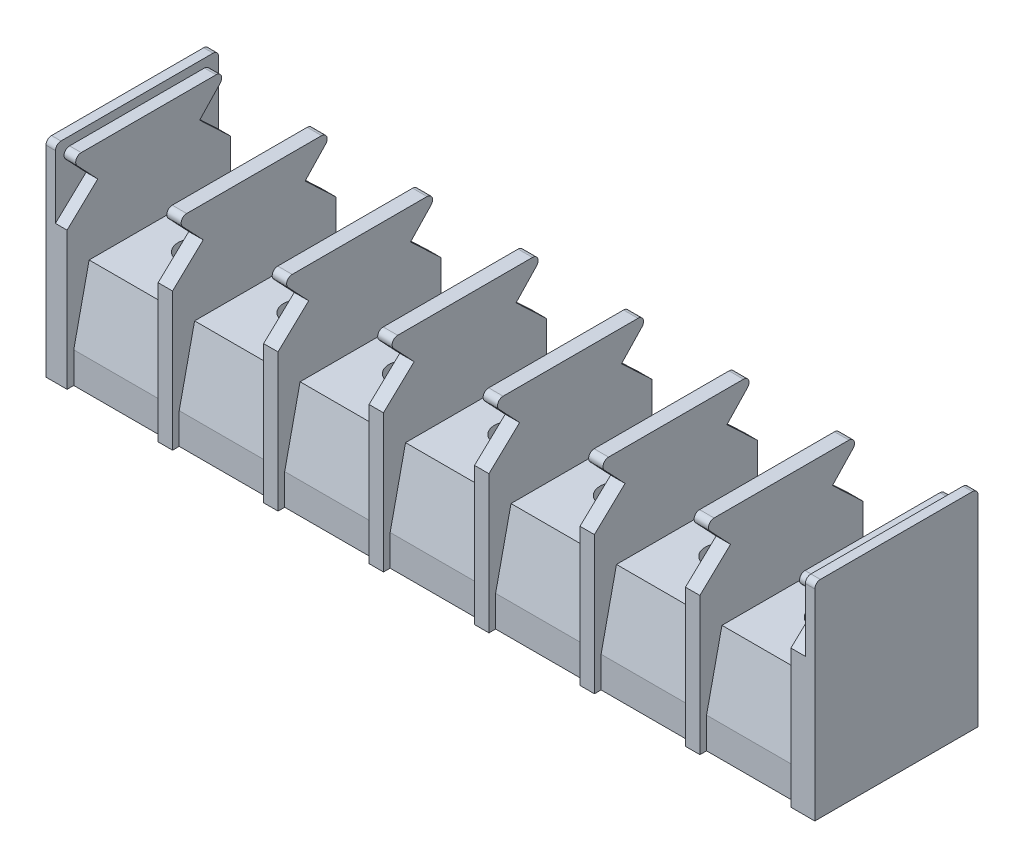
SolidWorks part; units mm, degrees
material "6061 Alloy"
ref_plane "Front Plane" through (0, 0, 0) normal (0, 0, 1) x (1, 0, 0)
ref_plane "Top Plane" through (0, 0, 0) normal (0, 1, 0) x (1, 0, 0)
ref_plane "Right Plane" through (0, 0, 0) normal (1, 0, 0) x (0, 0, -1)
sketch "Sketch1" plane through (0, 0, 0) normal (1, 0, 0) x (0, 0, -1)
  line L0 (6.75, 0) -> (7.35, 0) construction
  line L1 (-7.35, 0) -> (-6.75, 0) construction
  line L2 (-7.35, 0) -> (-7.35, 18.6) construction
  line L3 (-7.35, 18.6) -> (7.35, 18.6) construction
  line L4 (7.35, 0) -> (7.35, 18.6) construction
  line L5 (6.75, 0) -> (6.75, 2.79)
  line L6 (-6.75, 0) -> (-6.75, 2.79)
  line L7 (-6.75, 2.79) -> (-5.365, 9.1)
  line L8 (-5.365, 9.1) -> (5.365, 9.1)
  line L9 (5.365, 9.1) -> (6.75, 2.79)
  line L10 (-6.75, 0) -> (6.75, 0)
  line L11 (-6.75, 2.79) -> (6.75, 2.79) construction
  dimension "D1" = 18.6
  dimension "D2" = 14.7
  dimension "D3" = 1.2
  dimension "D4" = 10.73
  dimension "D5" = 9.1
  dimension "D6" = 2.79
extrude "Boss-Extrude1" add sketch "Sketch1" along normal mid plane 69.25
sketch "Sketch3" plane through (34.625, 0, 0) normal (1, 0, 0) x (0, 0, -1)
  line L0 (-6.75, 0) -> (-7.35, 0)
  line L1 (6.75, 0) -> (7.35, 0)
  line L2 (7.35, 0) -> (7.35, 18.1)
  line L3 (6.85, 18.6) -> (-6.85, 18.6)
  line L4 (-7.35, 18.1) -> (-7.35, 0)
  line L6 (-6.75, 0) -> (6.75, 0)
  line L7 (6.75, 0) -> (6.75, 2.79)
  line L8 (6.75, 2.79) -> (5.365, 9.1)
  line L9 (5.365, 9.1) -> (-5.365, 9.1)
  line L10 (-5.365, 9.1) -> (-6.75, 2.79)
  line L11 (-6.75, 2.79) -> (-6.75, 0)
  line L13 (6.75, 0) -> (6.75, 2.79)
  line L14 (6.75, 2.79) -> (5.365, 9.1)
  line L15 (5.365, 9.1) -> (-5.365, 9.1)
  line L16 (-5.365, 9.1) -> (-6.75, 2.79)
  line L17 (-6.75, 2.79) -> (-6.75, 0)
  arc A0 (6.85, 18.6) -> (7.35, 18.1) centre (6.85, 18.1) cw
  arc A1 (-6.85, 18.6) -> (-7.35, 18.1) centre (-6.85, 18.1) ccw
  point P13 (7.35, 18.6)
  point P16 (-7.35, 18.6)
  dimension "D4" = 0.5
  dimension "D2" = 18.6
  dimension "D3" = 14.7
  dimension "D1" = 0
extrude "Boss-Extrude2" add sketch "Sketch3" against normal blind 0.85
mirror "Mirror1" about plane through (0, 0, 0) normal (1, 0, 0) of "Boss-Extrude2"
sketch "Sketch4" plane through (33.775, 0, 0) normal (-1, 0, 0) x (0, 0, 1)
  line L0 (-7.35, 0) -> (-7.35, 18.1) construction
  line L1 (7.35, 18.1) -> (7.35, 0) construction
  line L2 (-6.75, 2.79) -> (-6.75, 0) construction
  line L3 (7.35, 12.42) -> (7.35, 0)
  line L4 (7.35, 0) -> (6.75, 0) construction
  line L5 (-5.365, 9.1) -> (-6.75, 2.79) construction
  line L6 (-7.35, 12.42) -> (-4.5889, 15.03)
  line L7 (7.35, 12.42) -> (4.5889, 15.03)
  line L8 (4.5889, 15.03) -> (6.4384, 16.9865)
  line L9 (-4.5889, 15.03) -> (-6.4384, 16.9865)
  line L10 (-6.75, 0) -> (-7.35, 0) construction
  line L11 (-7.35, 12.42) -> (7.35, 12.42) construction
  line L12 (-6.075, 17.83) -> (6.075, 17.83)
  line L13 (-7.35, 0) -> (-7.35, 12.42)
  line L14 (-6.75, 0) -> (-7.35, 0)
  line L15 (7.35, 0) -> (6.75, 0)
  line L16 (5.365, 9.1) -> (-5.365, 9.1) construction
  line L17 (-6.85, 18.6) -> (6.85, 18.6) construction
  line L18 (-6.75, 2.79) -> (-6.75, 0)
  line L19 (-5.365, 9.1) -> (-6.75, 2.79)
  line L20 (5.365, 9.1) -> (-5.365, 9.1)
  line L21 (6.75, 0) -> (6.75, 2.79) construction
  line L22 (6.75, 2.79) -> (5.365, 9.1) construction
  line L23 (6.75, 0) -> (6.75, 2.79)
  line L24 (6.75, 2.79) -> (5.365, 9.1)
  line L25 (-6.575, 12.42) -> (-6.575, 18.6) construction
  line L26 (-6.85, 18.6) -> (6.85, 18.6) construction
  line L27 (6.575, 12.42) -> (6.575, 18.6) construction
  arc A3 (6.075, 17.83) -> (6.4384, 16.9865) centre (6.075, 17.33) cw
  arc A4 (-6.075, 17.83) -> (-6.4384, 16.9865) centre (-6.075, 17.33) ccw
  arc A5 (-6.075, 17.83) -> (-6.4384, 16.9865) centre (-6.075, 17.33) ccw
  line M1 (6.75, 2.79) -> (6.75, 0)
  line M2 (6.75, 0) -> (7.35, 0)
  line M3 (7.35, 0) -> (7.35, 18.1)
  line M7 (-7.35, 18.1) -> (-7.35, 0)
  line M8 (-7.35, 0) -> (-6.75, 0)
  line M9 (-6.75, 0) -> (-6.75, 2.79)
  line M10 (-6.75, 2.79) -> (-5.365, 9.1)
  line M11 (-5.365, 9.1) -> (5.365, 9.1)
  line M12 (5.365, 9.1) -> (6.75, 2.79)
  dimension "D3" = 0.5
  dimension "D1" = 12.42
  dimension "D2" = 0.77
  dimension "D4" = 2.8
  dimension "D5" = 13.15
extrude "Boss-Extrude3" add sketch "Sketch4" along normal blind 1.3 contours L12 A4 L9 L6 L7 L8 A3 M7 M8 M9 M10 M11 M12 M1 M2 M3
pattern_linear "LPattern1" count 8 spacing 9.5 along (-1, 0, 0) of "Boss-Extrude3"
hole_wizard "M3.5x0.6 Tapped Hole1" positions "Sketch6" profile "Sketch5" tap size "M3.5x0.6" standard "ANSI Metric"
sketch "Sketch6" plane through (0, 9.1, 0) normal (0, 1, 0) x (1, 0, 0)
  line L12 (-32.725, 0) -> (-24.525, 0) construction
  line L14 (-24.525, 5.365) -> (-24.525, -5.365) construction
  line L15 (-23.225, 0) -> (-15.025, 0) construction
  line L17 (-15.025, 5.365) -> (-15.025, -5.365) construction
  line L21 (-4.225, 0) -> (3.975, 0) construction
  line L22 (-4.225, 5.365) -> (-4.225, -5.365) construction
  line L24 (5.275, 0) -> (13.475, 0) construction
  line L26 (13.475, 5.365) -> (13.475, -5.365) construction
  line L27 (14.775, 0) -> (22.975, 0) construction
  line L28 (14.775, 5.365) -> (14.775, -5.365) construction
  line L30 (24.275, 0) -> (32.475, 0) construction
  line L32 (32.475, 5.365) -> (32.475, -5.365) construction
  line L35 (-32.725, 5.365) -> (-32.725, -5.365) construction
  line L36 (-23.225, 5.365) -> (-23.225, -5.365) construction
  line L37 (3.975, 5.365) -> (3.975, -5.365) construction
  line L38 (5.275, 5.365) -> (5.275, -5.365) construction
  line L39 (22.975, 5.365) -> (22.975, -5.365) construction
  line L40 (24.275, 5.365) -> (24.275, -5.365) construction
  line L41 (-13.725, 0) -> (-5.525, 0) construction
  line L42 (-5.525, 5.365) -> (-5.525, -5.365) construction
  line L43 (-13.725, 5.365) -> (-13.725, -5.365) construction
  point P4 (-28.625, 0)
  point P6 (-19.125, 0)
  point P8 (0, 0)
  point P11 (-0.125, 0)
  point P13 (9.375, 0)
  point P15 (18.875, 0)
  point P17 (28.375, 0)
  point P134 (-9.625, 0)
sketch "Sketch5" plane through (-28.625, 9.1, 0) normal (1, 0, 0) x (0, 0, 1)
  line L0 (0, 0) -> (0, 8.8712)
  line L1 (0, 8.8712) -> (1.45, 8)
  line L2 (1.45, 8) -> (1.45, 0)
  line L5 (1.45, 0) -> (0, 0)
  line L10 (0, 8.8712) -> (-1.45, 8) construction
  line L11 (0, -6.35) -> (0, 107.95) construction
  dimension "Tap Drill Dia." = 2.9
  dimension "Tap Drill Depth" = 8
  dimension "Drill Angle" = 118
cosmetic thread "Hole Thread1" parameters "D1"=6, "D2"=3.5
cosmetic thread "Hole Thread2" parameters "D1"=6, "D2"=3.5
cosmetic thread "Hole Thread3" parameters "D1"=6, "D2"=3.5
cosmetic thread "Hole Thread4" parameters "D1"=6, "D2"=3.5
cosmetic thread "Hole Thread6" parameters "D1"=6, "D2"=3.5
cosmetic thread "Hole Thread7" parameters "D1"=6, "D2"=3.5
cosmetic thread "Hole Thread8" parameters "D1"=6, "D2"=3.5
cosmetic thread "Hole Thread9" parameters "D1"=6, "D2"=3.5
